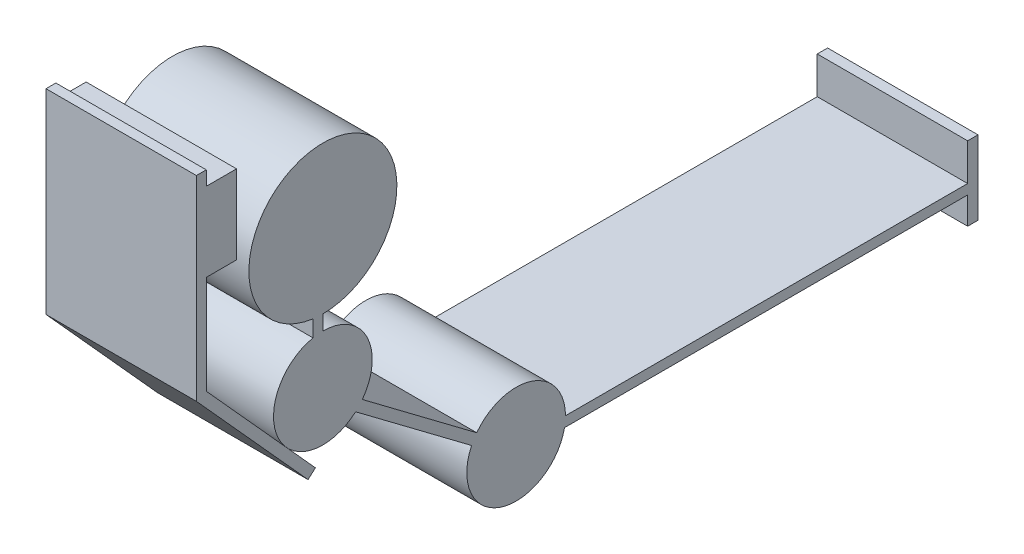
SolidWorks part; units mm, degrees
ref_plane "Front Plane" through (0, 0, 0) normal (0, 0, 1) x (1, 0, 0)
ref_plane "Top Plane" through (0, 0, 0) normal (0, 1, 0) x (1, 0, 0)
ref_plane "Right Plane" through (0, 0, 0) normal (1, 0, 0) x (0, 0, -1)
sketch "Sketch1" plane through (0, 0, 0) normal (1, 0, 0) x (0, 0, -1)
  line L0 (-1024.6887, 559.9719) -> (-1024.6887, 171.3916)
  line L1 (-1024.6887, 171.3916) -> (-803.5295, -73.5202)
  line L2 (-788.3729, 338.9044) -> (-788.3729, 58.9044)
  line L3 (-788.3729, 58.9044) -> (-396.7142, -235.55)
  line L4 (-396.7142, -235.55) -> (518.2858, -235.55)
  line L5 (-1024.6887, 531.0702) -> (-963.3729, 531.0702)
  line L6 (-963.3729, 531.0702) -> (-963.3729, 371.2204)
  line L7 (-963.3729, 371.2204) -> (-1024.6887, 371.2204)
  line L8 (-938.3729, 380.4298) -> (-938.3729, 338.9044)
  line L9 (518.2858, -160.55) -> (518.2858, -310.55)
  line L10 (-808.3729, 338.9044) -> (-808.3729, 48.9189)
  line L11 (-808.3729, 48.9189) -> (-403.3937, -255.55)
  line L12 (-403.3937, -255.55) -> (518.2858, -255.55)
  line L13 (-808.3729, 338.9044) -> (-788.3729, 338.9044)
  line L14 (-1044.6887, 559.9719) -> (-1044.6887, 163.6978)
  line L15 (-1044.6887, 163.6978) -> (-818.3731, -86.9242)
  line L16 (-1044.6887, 559.9719) -> (-1024.6887, 559.9719)
  line L17 (-818.3731, -86.9242) -> (-803.5295, -73.5202)
  line L18 (518.2858, -160.55) -> (539.2671, -160.55)
  line L19 (539.2671, -160.55) -> (539.2671, -310.55)
  line L20 (539.2671, -310.55) -> (518.2858, -310.55)
  circle A0 centre (-788.3729, 338.9044) radius 150
  circle A1 centre (-788.3729, 58.9044) radius 100
  circle A2 centre (-396.7142, -235.55) radius 100
  dimension "D1" = 300
  dimension "D2" = 200
  dimension "D3" = 200
  dimension "D4" = 25
  dimension "D5" = 61.3159
  dimension "D6" = 280
  dimension "D7" = 490
  dimension "D8" = 915
  dimension "D9" = 150
  dimension "D10" = 20
  dimension "D11" = 20
extrude "Boss-Extrude1" add sketch "Sketch1" along normal blind 304.8 contours L3 A1 L2 | L10 A1 L11 | L4 A2 L3 | L11 A2 L12 | A1 L2 A0 L10 | A2 L3 A1 L11 | L2 A1 L10 L11 L3 | L3 A2 L11 L12 L4 | A2 L12 L9 L4 | A0 L10 L13 L2 | L10 A0 L2 L13 | L7 L6 L5 L0
